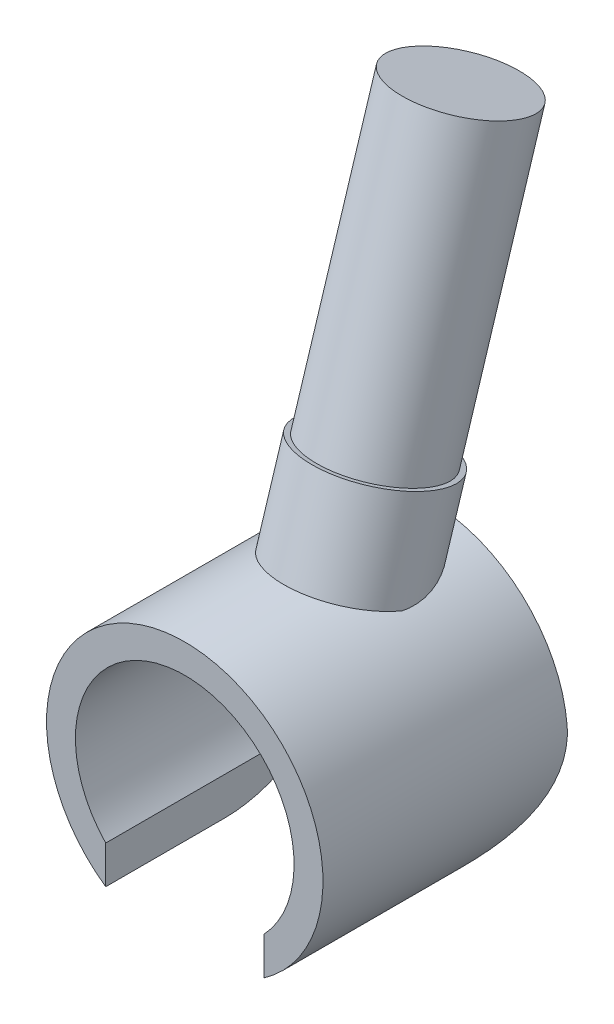
SolidWorks part; units mm, degrees
ref_plane "정면" through (0, 0, 0) normal (0, 0, 1) x (1, 0, 0)
ref_plane "평면" through (0, 0, 0) normal (0, 1, 0) x (1, 0, 0)
ref_plane "우측면" through (0, 0, 0) normal (1, 0, 0) x (0, 0, -1)
sketch "스케치1" plane through (0, 0, 0) normal (0, 0, 1) x (1, 0, 0)
  line L1 (-1.395, -1.3337) -> (-1.395, -2.0019)
  line L2 (1.395, -1.3337) -> (1.395, -2.0019)
  arc A0 (1.395, -1.3337) -> (-1.395, -1.3337) centre (0, 0) ccw
  arc A1 (1.395, -2.0019) -> (-1.395, -2.0019) centre (0, 0) ccw
  dimension "D1" = 1.93
  dimension "D2" = 2.44
  dimension "D3" = 2.79
extrude "보스-돌출2" add sketch "스케치1" along normal mid plane 4.32
sketch "스케치2" plane through (0, 0, 0) normal (1, 0, 0) x (0, 0, -1)
  line L3 (2.16, -2.0019) -> (-0.06, -2.0019)
  line L4 (2.16, 0.2181) -> (2.16, -2.0019)
  arc A1 (2.16, 0.2181) -> (-0.06, -2.0019) centre (-0.06, 0.2181) cw
  dimension "D1" = 2.22
  dimension "D2" = 2.16
  dimension "D3" = 2.0019
extrude "컷-돌출1" cut sketch "스케치2" against normal mid plane 5
sketch "스케치3" plane through (0, 0, 0) normal (1, 0, 0) x (0, 0, -1)
  line L0 (2.7128, 8.54) -> (0.7058, 2.0923)
  line L1 (-2.16, 2.44) -> (-2.16, -2.0019) construction
  line L4 (0.7058, 2.0923) -> (2.7128, 8.54) construction
  line L5 (1.6816, 8.861) -> (2.7128, 8.54)
  line L7 (-0.4114, 2.44) -> (0.0829, 4.0277)
  line L8 (-0.3031, 2.7877) -> (1.5957, 8.8877) construction
  line L9 (-0.4114, 2.44) -> (0.7058, 2.0923)
  line L10 (0.814, 2.44) -> (2.7128, 8.54) construction
  line L15 (0.0829, 4.0277) -> (0.1688, 4.001)
  line L17 (0.1688, 4.001) -> (1.6816, 8.861)
  dimension "D1" = 17.29
  dimension "D2" = 0.0829
  dimension "D3" = 0.1688
  dimension "D4" = 0.7058
  dimension "D5" = 1.6816
  dimension "D6" = 2.7128
  dimension "D7" = 2.0923
revolve "회전1" add sketch "스케치3" angle 360 about L0
sketch "스케치4" plane through (0, 0, 0) normal (0, 0, 1) x (1, 0, 0)
  circle A2 centre (0, 0) radius 1.93
  dimension "D1" = 3.86
extrude "컷-돌출2" cut sketch "스케치4" against normal up to next
